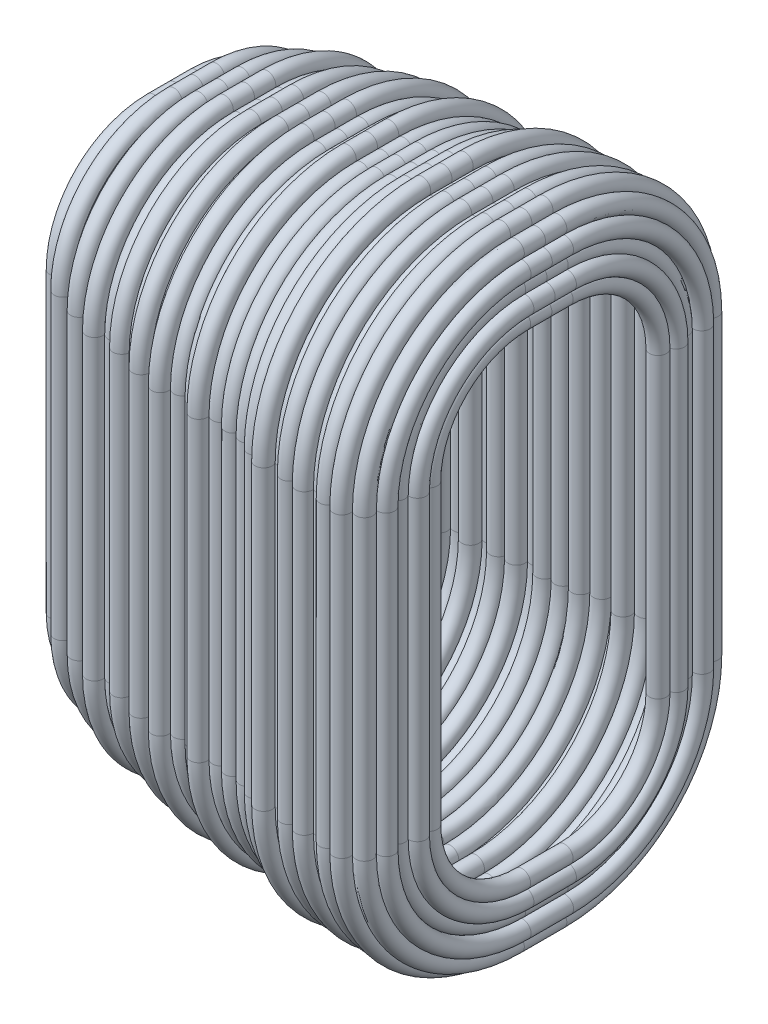
SolidWorks part; units mm, degrees
ref_plane "Alzado" through (0, 0, 0) normal (0, 0, 1) x (1, 0, 0)
ref_plane "Planta" through (0, 0, 0) normal (0, 1, 0) x (1, 0, 0)
ref_plane "Vista lateral" through (0, 0, 0) normal (1, 0, 0) x (0, 0, -1)
sketch "Croquis1" plane through (0, 0, 0) normal (1, 0, 0) x (0, 0, -1)
  line L0 (0, -2.65) -> (0, 2.65) construction
  line L1 (-0.25, 2.55) -> (0.25, 2.55)
  line L2 (-1.05, 1.75) -> (-1.05, -1.75)
  line L3 (-0.25, -2.55) -> (0.25, -2.55)
  line L4 (1.05, 1.75) -> (1.05, -1.75)
  line L5 (-1.05, 2.55) -> (1.05, -2.55) construction
  line L6 (-1.05, -2.55) -> (1.05, 2.55) construction
  arc A0 (-1.05, -1.75) -> (-0.25, -2.55) centre (-0.25, -1.75) ccw
  arc A1 (0.25, -2.55) -> (1.05, -1.75) centre (0.25, -1.75) ccw
  arc A2 (0.25, 2.55) -> (1.05, 1.75) centre (0.25, 1.75) cw
  arc A3 (-0.25, 2.55) -> (-1.05, 1.75) centre (-0.25, 1.75) ccw
  point P3 (0, 0)
  dimension "D1" = 5.1
  dimension "D3" = 0.8
  dimension "D2" = 2.1
sketch "Croquis2" plane through (0, 0, 0) normal (0, 0, 1) x (1, 0, 0)
  line L0 (-2.25, 2.6007) -> (2.25, 2.6007) construction
  arc A0 (-2.1684, 2.8107) -> (-2.1453, 2.6269) centre (-2.1942, 2.7141) ccw
  arc A1 (-2.1164, 2.777) -> (-1.9961, 2.8407) centre (-2.0906, 2.8736) ccw
  arc A2 (-1.9961, 2.8407) -> (-1.8474, 2.9584) centre (-1.9021, 2.8747) ccw
  arc A3 (-1.8474, 2.9584) -> (-1.7665, 3.0081) centre (-1.853, 3.0582) ccw
  arc A4 (-1.7665, 3.0081) -> (-1.5856, 3.0738) centre (-1.6667, 3.0153) ccw
  arc A5 (-1.5856, 3.0738) -> (-1.4625, 3.1199) centre (-1.5505, 3.1674) ccw
  arc A6 (-1.4625, 3.1199) -> (-1.285, 3.1879) centre (-1.3627, 3.1249) ccw
  arc A7 (-1.285, 3.1879) -> (-1.1838, 3.2123) centre (-1.2544, 3.2831) ccw
  arc A8 (-1.1838, 3.2123) -> (-0.9906, 3.2192) centre (-1.0863, 3.19) ccw
  arc A9 (-0.9906, 3.2192) -> (-0.8363, 3.2478) centre (-0.9247, 3.2944) ccw
  arc A10 (-0.8363, 3.2478) -> (-0.6486, 3.3008) centre (-0.7364, 3.253) ccw
  arc A11 (-0.6486, 3.3008) -> (-0.5258, 3.3234) centre (-0.6013, 3.3889) ccw
  arc A12 (-0.5258, 3.3234) -> (-0.3414, 3.3645) centre (-0.4264, 3.3118) ccw
  arc A13 (-0.3414, 3.3645) -> (-0.2404, 3.3819) centre (-0.3055, 3.4578) ccw
  arc A14 (-0.2404, 3.3819) -> (-0.0445, 3.342) centre (-0.1428, 3.3603) ccw
  arc A15 (-0.0445, 3.342) -> (0.141, 3.4169) centre (0.0481, 3.3798) ccw
  arc A16 (0.141, 3.4169) -> (0.2579, 3.4263) centre (0.1929, 3.5024) ccw
  arc A17 (0.2579, 3.4263) -> (0.4535, 3.385) centre (0.3556, 3.4051) ccw
  arc A18 (0.4535, 3.385) -> (0.6334, 3.4134) centre (0.537, 3.4401) ccw
  arc A19 (0.6334, 3.4134) -> (0.8236, 3.4668) centre (0.7243, 3.4551) ccw
  arc A20 (1.7992, 3.5186) -> (1.9228, 3.5847) centre (1.8273, 3.6145) ccw
  arc A21 (1.9228, 3.5847) -> (2.0743, 3.5611) centre (2.0084, 3.6363) ccw
  arc A22 (2.0743, 3.5611) -> (2.1838, 3.4327) centre (2.1699, 3.5318) ccw
  arc A23 (-1.9965, 2.9076) -> (-2.1684, 2.8107) centre (-2.0906, 2.8736) ccw
  arc A24 (-1.9076, 2.9745) -> (-1.9965, 2.9076) centre (-1.9021, 2.8747) ccw
  arc A25 (-1.7532, 3.0655) -> (-1.9076, 2.9745) centre (-1.853, 3.0582) ccw
  arc A26 (-1.6316, 3.1089) -> (-1.7532, 3.0655) centre (-1.6667, 3.0153) ccw
  arc A27 (-1.4507, 3.1725) -> (-1.6316, 3.1089) centre (-1.5505, 3.1674) ccw
  arc A28 (-1.3321, 3.2201) -> (-1.4507, 3.1725) centre (-1.3627, 3.1249) ccw
  arc A29 (-1.1569, 3.2608) -> (-1.3321, 3.2201) centre (-1.2544, 3.2831) ccw
  arc A30 (-1.0204, 3.2652) -> (-1.1569, 3.2608) centre (-1.0863, 3.19) ccw
  arc A31 (-0.8249, 3.2997) -> (-1.0204, 3.2652) centre (-0.9247, 3.2944) ccw
  arc A32 (-0.6891, 3.3411) -> (-0.8249, 3.2997) centre (-0.7364, 3.253) ccw
  arc A33 (-0.502, 3.3773) -> (-0.6891, 3.3411) centre (-0.6013, 3.3889) ccw
  arc A34 (-0.3906, 3.4052) -> (-0.502, 3.3773) centre (-0.4264, 3.3118) ccw
  arc A35 (-0.2079, 3.4362) -> (-0.3906, 3.4052) centre (-0.3055, 3.4578) ccw
  arc A36 (-0.0502, 3.3981) -> (-0.2079, 3.4362) centre (-0.1428, 3.3603) ccw
  arc A37 (0.1, 3.4653) -> (-0.0502, 3.3981) centre (0.0481, 3.3798) ccw
  arc A38 (0.2906, 3.4811) -> (0.1, 3.4653) centre (0.1929, 3.5024) ccw
  arc A39 (0.4391, 3.4601) -> (0.2906, 3.4811) centre (0.3556, 3.4051) ccw
  arc A40 (0.6279, 3.4818) -> (0.4391, 3.4601) centre (0.537, 3.4401) ccw
  arc A41 (0.7994, 3.5211) -> (0.6279, 3.4818) centre (0.7243, 3.4551) ccw
  arc A42 (0.9698, 3.6031) -> (0.7994, 3.5211) centre (0.8987, 3.5328) ccw
  arc A43 (1.157, 3.5688) -> (0.9698, 3.6031) centre (1.0689, 3.6161) ccw
  arc A44 (0.8236, 3.4668) -> (0.9979, 3.5458) centre (0.8987, 3.5328) ccw
  arc A45 (0.9979, 3.5458) -> (1.1133, 3.5265) centre (1.0689, 3.6161) ccw
  arc A46 (1.1133, 3.5265) -> (1.2904, 3.5248) centre (1.2014, 3.4792) ccw
  arc A47 (1.2904, 3.5248) -> (1.4555, 3.5944) centre (1.3557, 3.6006) ccw
  arc A48 (1.4555, 3.5944) -> (1.5997, 3.5334) centre (1.5518, 3.6212) ccw
  arc A49 (1.5997, 3.5334) -> (1.7992, 3.5186) centre (1.6994, 3.5255) ccw
  arc A50 (1.2667, 3.5549) -> (1.157, 3.5688) centre (1.2014, 3.4792) ccw
  arc A51 (1.452, 3.6273) -> (1.2667, 3.5549) centre (1.3557, 3.6006) ccw
  arc A52 (1.6515, 3.6133) -> (1.452, 3.6273) centre (1.5518, 3.6212) ccw
  arc A53 (1.7275, 3.6214) -> (1.6515, 3.6133) centre (1.6994, 3.5255) ccw
  arc A54 (1.913, 3.6661) -> (1.7275, 3.6214) centre (1.8273, 3.6145) ccw
  arc A55 (2.104, 3.6069) -> (1.913, 3.6661) centre (2.0084, 3.6363) ccw
  arc A56 (2.2178, 2.9451) -> (2.3094, 2.9243) centre (2.2441, 2.8486) ccw
  arc A57 (2.3094, 2.9243) -> (2.274, 3.1204) centre (2.2831, 3.0208) ccw
  arc A58 (2.1838, 3.4327) -> (2.2068, 3.2668) centre (2.2494, 3.3573) ccw
  arc A59 (2.2068, 3.2668) -> (2.1957, 3.0693) centre (2.1866, 3.1689) ccw
  arc A60 (2.1957, 3.0693) -> (2.2178, 2.9451) centre (2.2831, 3.0208) ccw
  arc A61 (-2.1159, 2.652) -> (-2.1164, 2.777) centre (-2.1942, 2.7141) ccw
  arc A62 (-2.1453, 2.6269) -> (-2.1159, 2.652) centre (-2.0669, 2.5648) ccw
  arc A63 (2.2356, 3.4563) -> (2.104, 3.6069) centre (2.1699, 3.5318) ccw
  arc A64 (2.2292, 3.2593) -> (2.2356, 3.4563) centre (2.2494, 3.3573) ccw
  arc A65 (2.274, 3.1204) -> (2.2292, 3.2593) centre (2.1866, 3.1689) ccw
  dimension "D1" = 0.2
  dimension "D3" = 0.2
  dimension "D2" = 4.5
sweep "Barrer1" add profiles "Croquis2" path "Croquis1"
